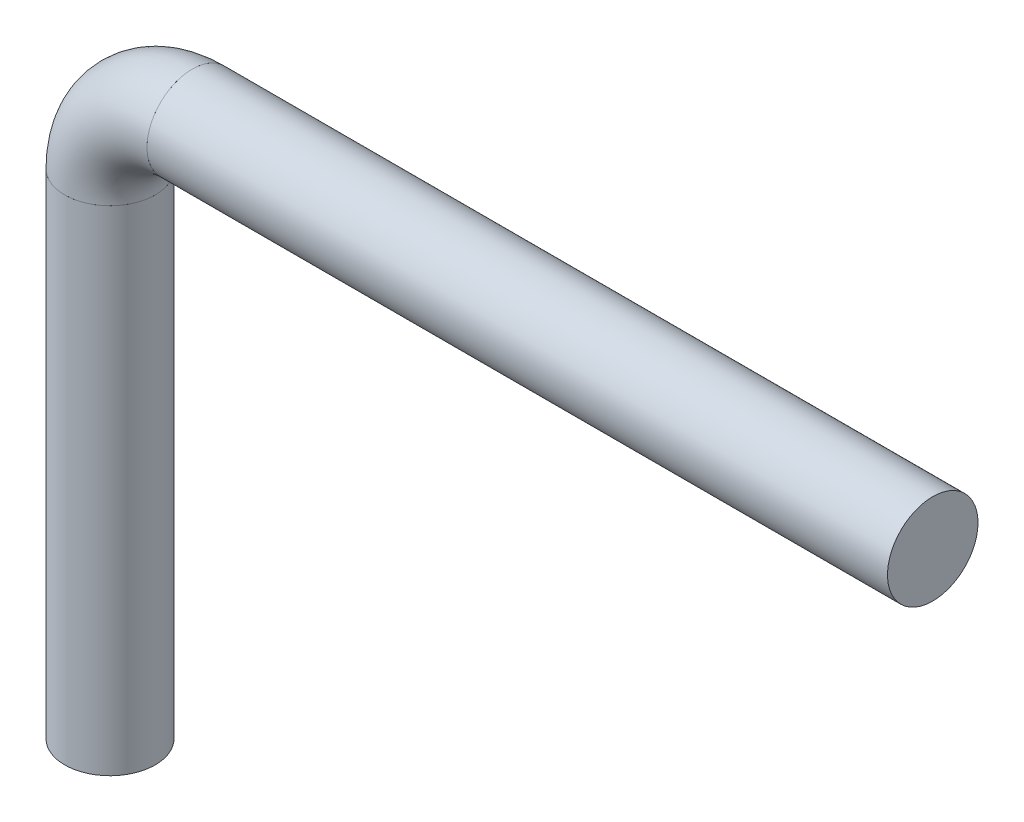
SolidWorks part; units mm, degrees
ref_plane "Front Plane" through (0, 0, 0) normal (0, 0, 1) x (1, 0, 0)
ref_plane "Top Plane" through (0, 0, 0) normal (0, 1, 0) x (1, 0, 0)
ref_plane "Right Plane" through (0, 0, 0) normal (1, 0, 0) x (0, 0, -1)
ref_plane "Plane1" through (1, 0, 0) normal (1, 0, 0) x (0, 0, -1)
ref_plane "Plane2" through (0, 6, 0) normal (0, -1, 0) x (-1, 0, 0)
sketch "Sketch6" plane through (0, 6, 0) normal (0, -1, 0) x (-1, 0, 0)
  circle A0 centre (0, 0) radius 0.55
  dimension "D1" = 1.1
extrude "Boss-Extrude1" add sketch "Sketch6" along normal blind 6
sketch "Sketch11" plane through (1, 0, 0) normal (1, 0, 0) x (0, 0, -1)
  circle A0 centre (0, 7) radius 0.55
  dimension "D1" = 1.1
extrude "Boss-Extrude2" add sketch "Sketch11" along normal blind 9
ref_plane "Plane3" through (0, 0, 0) normal (0, 0, -1) x (-1, 0, 0)
sketch "Sketch17" plane through (0, 0, 0) normal (0, 0, -1) x (-1, 0, 0)
  line L0 (-10, 7.25) -> (-10, 7)
  line L1 (-10, 7) -> (-1, 7)
  line L2 (-1, 7) -> (-1, 7.25)
  line L3 (-1, 7.25) -> (-10, 7.25)
  line L4 (-10, 7) -> (-1, 7) construction
sketch "Sketch20" plane through (0, 0, 0) normal (0, 0, -1) x (-1, 0, 0)
  line L0 (-1, 6.55) -> (-1, 6) construction
  line L3 (-1, 6) -> (-0.55, 6) construction
sketch "Sketch22" plane through (1, 0, 0) normal (-1, 0, 0) x (0, 0, 1)
  line L0 (-0.2809, 6) -> (0.2809, 6) construction
  circle A0 centre (0, 7) radius 0.55
  point P6 (0, 6.0632)
  point P7 (0, 6)
  dimension "D1" = 1.1
  dimension "D2" = 1
revolve "Revolve1" add sketch "Sketch22" angle 90 about L0
